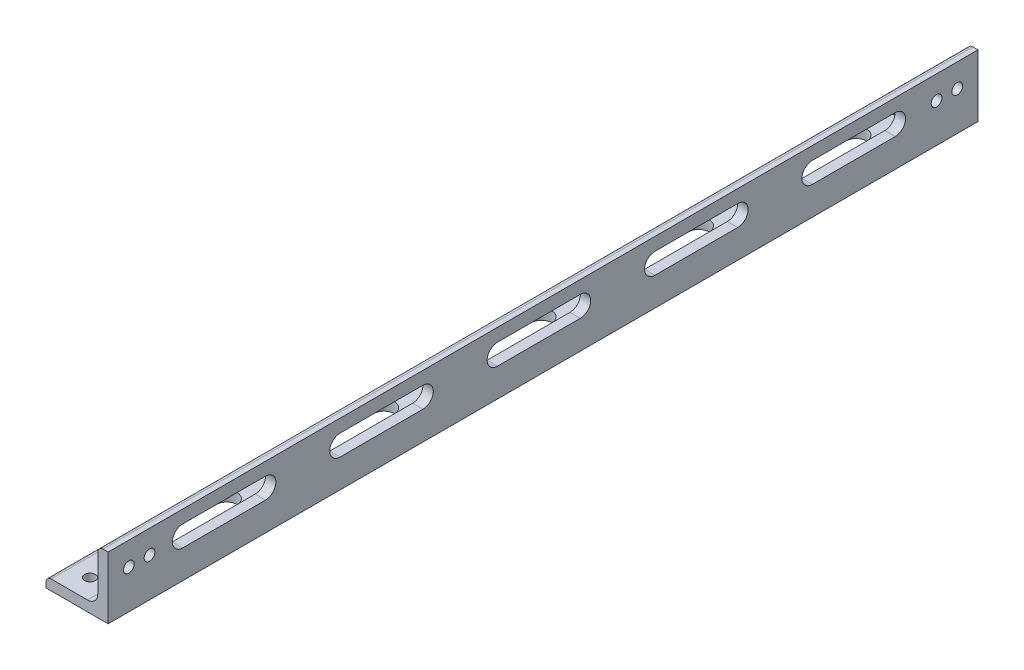
SolidWorks part; units mm, degrees
material "6061-T6 (SS)"
ref_plane "Front Plane" through (0, 0, 0) normal (0, 0, 1) x (1, 0, 0)
ref_plane "Top Plane" through (0, 0, 0) normal (0, 1, 0) x (1, 0, 0)
ref_plane "Right Plane" through (0, 0, 0) normal (1, 0, 0) x (0, 0, -1)
sketch "Sketch0" plane through (0, 0, 0) normal (0, 0, 1) x (1, 0, 0)
  line L0 (-9.525, -9.525) -> (9.525, -9.525)
  line L1 (9.525, -9.525) -> (9.525, 9.525)
  line L2 (9.525, 0) -> (0, 0) construction
  line L3 (0, 0) -> (0, -9.525) construction
  line L4 (6.35, -3.175) -> (6.35, 9.525) construction
  line L5 (3.175, -6.35) -> (-9.525, -6.35) construction
  arc A0 (6.35, -3.175) -> (3.175, -6.35) centre (3.175, -3.175) cw
  point P3 (5.4201, -5.4201)
  dimension "Inside Corner Radius" = 3.175
  dimension "Outside Height" = 19.05
  dimension "Inside Height" = 15.875
  dimension "Inside Width" = 15.875
  dimension "Wall Thickness" = 3.175
  dimension "D1" = 3.175
  dimension "Outside Width" = 19.05
sketch "Sketch1" plane through (0, 0, 0) normal (1, 0, 0) x (0, 0, -1)
  line L0 (133.35, 0) -> (-133.35, 0)
  point P4 (0, 0)
  dimension "Length" = 266.7
sketch "Sketch2" plane through (0, 0, 0) normal (0, 0, 1) x (1, 0, 0)
  line L0 (-9.525, -9.525) -> (9.525, -9.525)
  line L1 (9.525, -9.525) -> (9.525, 9.525)
  line L2 (9.525, 9.525) -> (6.35, 9.525) construction
  line L3 (6.35, 7.9375) -> (6.35, -3.175)
  line L4 (3.175, -6.35) -> (-7.9375, -6.35)
  line L5 (-9.525, -9.525) -> (-9.525, -6.35) construction
  line L6 (7.9375, 9.525) -> (9.525, 9.525)
  line L7 (-9.525, -7.9375) -> (-9.525, -9.525)
  line L8 (9.525, 0) -> (0, 0) construction
  line L9 (0, 0) -> (0, -9.525) construction
  arc A0 (6.35, 7.9375) -> (7.9375, 9.525) centre (7.9375, 7.9375) cw
  arc A1 (-9.525, -7.9375) -> (-7.9375, -6.35) centre (-7.9375, -7.9375) cw
  arc A2 (6.35, -3.175) -> (3.175, -6.35) centre (3.175, -3.175) cw
  dimension "Inside Radius" = 3.175
  dimension "Height" = 19.05
  dimension "Width" = 19.05
  dimension "Thickness" = 3.175
extrude "Boss-Extrude1" add sketch "Sketch2" along normal mid plane 266.7
sketch "Break Locations" plane through (0, 0, 0) normal (1, 0, 0) x (0, 0, -1)
  line L0 (-113.919, 0) -> (113.919, 0)
  line L1 (-133.35, -9.525) -> (-133.35, 9.525) construction
  line L2 (133.35, -9.525) -> (133.35, 9.525) construction
  point P0 (-117.1575, 0)
  point P1 (117.1575, 0)
  point P10 (0, 0)
  point P11 (113.919, 0)
  point P13 (-113.919, 0)
  dimension "D1" = 16.1925
  dimension "D2" = 16.1925
  dimension "D3" = 19.431
sketch "Sketch3" plane through (0, -6.35, 0) normal (0, 1, 0) x (1, 0, 0)
  line L0 (-2.3812, 133.35) -> (-2.3812, 127) construction
  line L1 (3.175, 133.35) -> (-7.9375, 133.35) construction
  line L2 (-2.3812, 127) -> (-2.3812, 120.65) construction
  line L3 (3.175, 0) -> (-7.9375, 0) construction
  line L4 (3.175, -133.35) -> (3.175, 133.35) construction
  line L5 (-7.9375, -133.35) -> (-7.9375, 133.35) construction
  circle A0 centre (-2.3812, 127) radius 1.651
  circle A1 centre (-2.3812, 120.65) radius 1.651
  circle A2 centre (-2.3812, -120.65) radius 1.651
  circle A3 centre (-2.3812, -127) radius 1.651
  dimension "D2" = 3.302
  dimension "D4" = 3.302
  dimension "D1" = 6.35
  dimension "D3" = 6.35
extrude "Cut-Extrude1" cut sketch "Sketch3" against normal through all
sketch "Sketch4" plane through (6.35, 0, 0) normal (-1, 0, 0) x (0, 0, 1)
  line L0 (-133.35, 2.3813) -> (-127, 2.3813) construction
  line L1 (-127, 2.3813) -> (-120.65, 2.3812) construction
  line L2 (0, 7.9375) -> (0, -3.175) construction
  line L3 (-133.35, 7.9375) -> (-133.35, -3.175) construction
  line L4 (133.35, 7.9375) -> (-133.35, 7.9375) construction
  line L5 (133.35, -3.175) -> (-133.35, -3.175) construction
  circle A0 centre (-127, 2.3813) radius 1.651
  circle A1 centre (-120.65, 2.3812) radius 1.651
  circle A2 centre (120.65, 2.3812) radius 1.651
  circle A3 centre (127, 2.3813) radius 1.651
  dimension "D1" = 3.302
  dimension "D3" = 3.302
  dimension "D2" = 6.35
  dimension "D4" = 6.35
extrude "Cut-Extrude2" cut sketch "Sketch4" against normal through all
sketch "Sketch5" plane through (6.35, 0, 0) normal (-1, 0, 0) x (0, 0, 1)
  line L0 (-120.65, 2.3812) -> (-107.95, 2.3812) construction
  line L2 (-107.95, 5.5562) -> (-82.55, 5.5562)
  line L3 (-107.95, -0.7938) -> (-82.55, -0.7938)
  arc A0 (-107.95, 5.5562) -> (-107.95, -0.7938) centre (-107.95, 2.3812) ccw
  arc A1 (-82.55, -0.7938) -> (-82.55, 5.5562) centre (-82.55, 2.3812) ccw
  dimension "D1" = 3.175
  dimension "D3" = 3.175
  dimension "D2" = 25.4
extrude "Cut-Extrude3" cut sketch "Sketch5" against normal through all
pattern_linear "LPattern1" count 5 spacing 48.26 along (0, 0, 1) of "Cut-Extrude3"
sketch "Sketch6" plane through (0, -6.35, 0) normal (0, 1, 0) x (1, 0, 0)
  line L0 (-2.3812, 120.65) -> (-2.3812, 107.95) construction
  line L2 (-5.5562, 107.95) -> (-5.5562, 82.55)
  line L3 (0.7938, 107.95) -> (0.7938, 82.55)
  arc A0 (-5.5562, 107.95) -> (0.7938, 107.95) centre (-2.3812, 107.95) cw
  arc A1 (-5.5562, 82.55) -> (0.7938, 82.55) centre (-2.3812, 82.55) ccw
  dimension "D1" = 3.175
  dimension "D2" = 3.175
  dimension "D3" = 25.4
extrude "Cut-Extrude4" cut sketch "Sketch6" against normal through all
pattern_linear "LPattern2" count 5 spacing 48.26 along (0, 0, 1) of "Cut-Extrude4"
equation "\"D1@Break Locations\" = .85 * \"Height@Sketch2\""
equation "\"D2@Break Locations\"=\"D1@Break Locations\""
equation "\"Thickness@Sketch2\"=\"wall thickness@sketch0\""
equation "\"Height@Sketch2\"=\"outside height@sketch0\""
equation "\"Width@Sketch2\"=\"outside width@sketch0\""
equation "\"Inside Radius@Sketch2\"=\"inside corner radius@sketch0\""
equation "\"Length@Boss-Extrude1\"=\"length@sketch1\""
equation "\"D3@Break Locations\"=\"D2@Break Locations\"*1.2"
equation "\"D1@Sketch0\"=\"Wall Thickness@Sketch0\""
